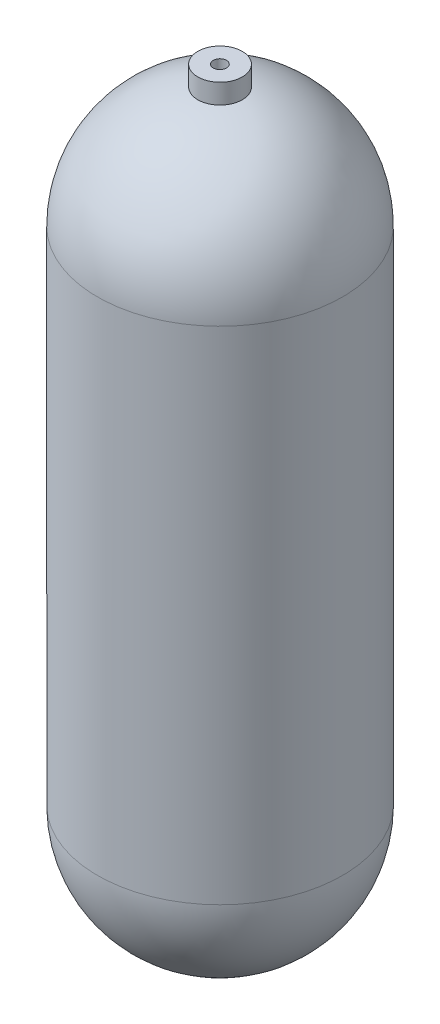
SolidWorks part; units mm, degrees
material "A-Glass Fiber"
ref_plane "Front Plane" through (0, 0, 0) normal (0, 0, 1) x (1, 0, 0)
ref_plane "Top Plane" through (0, 0, 0) normal (0, 1, 0) x (1, 0, 0)
ref_plane "Right Plane" through (0, 0, 0) normal (1, 0, 0) x (0, 0, -1)
sketch "Sketch1" plane through (0, 0, 0) normal (0, 0, 1) x (1, 0, 0)
  line L0 (-277.9989, 0) -> (285.3595, 0) construction
  line L1 (87.63, 445.77) -> (87.63, 87.63)
  line L2 (-223.1734, 533.4) -> (246.1876, 533.4) construction
  line L3 (0, -16.2482) -> (0, 0) construction
  line L4 (84.455, 445.77) -> (84.455, 87.63)
  line L5 (0, 533.4) -> (0, 540.8646) construction
  line L6 (0, 530.225) -> (0, 533.4)
  line L7 (0, 3.175) -> (0, 0)
  arc A0 (0, 0) -> (87.63, 87.63) centre (0, 87.63) ccw
  arc A1 (87.63, 445.77) -> (0, 533.4) centre (0, 445.77) ccw
  arc A2 (84.455, 445.77) -> (0, 530.225) centre (0, 445.77) ccw
  arc A3 (0, 3.175) -> (84.455, 87.63) centre (0, 87.63) ccw
  dimension "D1" = 533.4
  dimension "D2" = 87.63
  dimension "D3" = 3.175
revolve "Revolve1" add sketch "Sketch1" angle 360 about L5
ref_plane "Plane1" through (0, 533.4, 0) normal (0, 1, 0) x (1, 0, 0)
sketch "Sketch2" plane through (0, 533.4, 0) normal (0, 1, 0) x (1, 0, 0)
  circle A0 centre (0, 0) radius 15.875
  dimension "D1" = 31.75
extrude "Boss-Extrude1" add sketch "Sketch2" along normal blind 12.7 and the other way up to next contours A0
sketch "Sketch3" plane through (0, 546.1, 0) normal (0, 1, 0) x (1, 0, 0)
  line L0 (0, 28.2988) -> (0, -59.228) construction
  line L1 (-76.1012, 0) -> (75.6366, 0) construction
hole_wizard "3/8 (0.375) Diameter Hole1" positions "3DSketch1" profile "Sketch5" hole size "3/8" standard "ANSI Inch"
sketch3d "3DSketch1"
  point P0 (-0.0532, 546.1, 0.0938)
sketch "Sketch5" plane through (-0.0532, 546.1, 0.0938) normal (1, 0, 0) x (0, 0, 1)
  line L0 (0, 0) -> (0, 28.2616)
  line L1 (0, 28.2616) -> (4.7625, 25.4)
  line L2 (4.7625, 25.4) -> (4.7625, 0)
  line L5 (4.7625, 0) -> (0, 0)
  line L10 (0, 28.2616) -> (-4.7625, 25.4) construction
  line L11 (0, -6.35) -> (0, 107.95) construction
  dimension "Hole Dia." = 9.525
  dimension "Hole Depth" = 25.4
  dimension "Drill Angle" = 118
